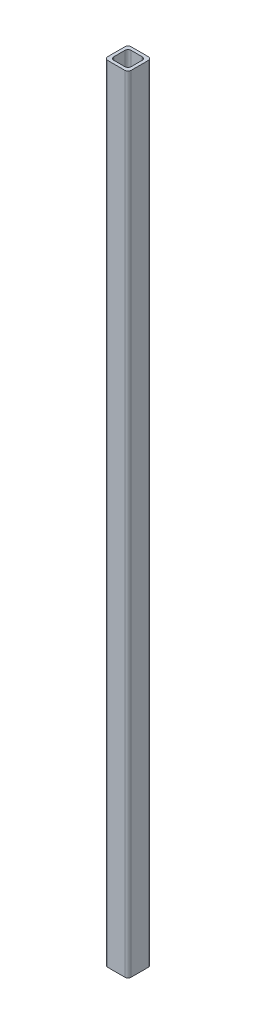
SolidWorks part; units mm, degrees
ref_plane "Front Plane" through (0, 0, 0) normal (0, 0, 1) x (1, 0, 0)
ref_plane "Top Plane" through (0, 0, 0) normal (0, 1, 0) x (1, 0, 0)
ref_plane "Right Plane" through (0, 0, 0) normal (1, 0, 0) x (0, 0, -1)
sketch "Sketch1" plane through (0, 0, 0) normal (0, 1, 0) x (1, 0, 0)
  line L1 (11, 15) -> (-11, 15)
  line L2 (15, 11) -> (15, -11)
  line L3 (11, -15) -> (-11, -15)
  line L4 (-15, 11) -> (-15, -11)
  line L5 (7, 11) -> (-7, 11)
  line L6 (11, 7) -> (11, -7)
  line L7 (7, -11) -> (-7, -11)
  line L8 (-11, 7) -> (-11, -7)
  line L9 (11, 11) -> (-11, -11) construction
  line L10 (11, -11) -> (-11, 11) construction
  arc A0 (-15, 11) -> (-11, 15) centre (-11, 11) cw
  arc A1 (11, 15) -> (15, 11) centre (11, 11) cw
  arc A2 (15, -11) -> (11, -15) centre (11, -11) cw
  arc A3 (-15, -11) -> (-11, -15) centre (-11, -11) ccw
  arc A4 (7, 11) -> (11, 7) centre (7, 7) cw
  arc A5 (11, -7) -> (7, -11) centre (7, -7) cw
  arc A6 (-7, -11) -> (-11, -7) centre (-7, -7) cw
  arc A7 (-7, 11) -> (-11, 7) centre (-7, 7) ccw
  point P0 (0, 0)
  point P14 (0, 0)
  dimension "D1" = 4
  dimension "D2" = 4
  dimension "D3" = 4
extrude "Boss-Extrude1" add sketch "Sketch1" along normal blind 1000
